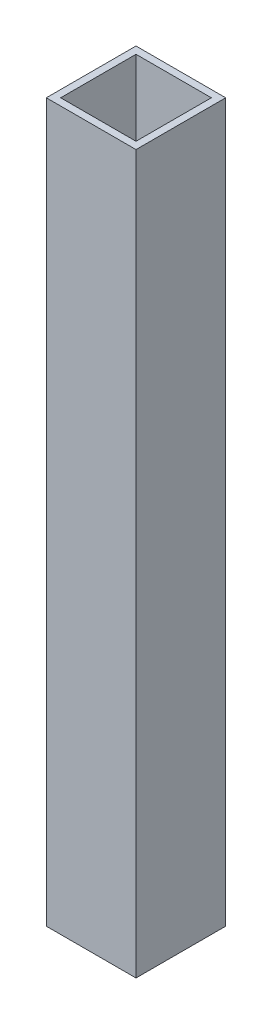
SolidWorks part; units mm, degrees
ref_plane "Front Plane" through (0, 0, 0) normal (0, 0, 1) x (1, 0, 0)
ref_plane "Top Plane" through (0, 0, 0) normal (0, 1, 0) x (1, 0, 0)
ref_plane "Right Plane" through (0, 0, 0) normal (1, 0, 0) x (0, 0, -1)
sketch "Sketch1" plane through (0, 0, 0) normal (0, 1, 0) x (1, 0, 0)
  line L0 (-12.5, 12.5) -> (12.5, -12.5) construction
  line L1 (-12.5, 12.5) -> (12.5, 12.5)
  line L2 (-12.5, 12.5) -> (-12.5, -12.5)
  line L3 (-12.5, -12.5) -> (12.5, -12.5)
  line L4 (12.5, 12.5) -> (12.5, -12.5)
  line L5 (-10.5, 10.5) -> (-10.5, -10.5)
  line L6 (-10.5, -10.5) -> (10.5, -10.5)
  line L7 (10.5, 10.5) -> (10.5, -10.5)
  line L8 (-10.5, 10.5) -> (10.5, 10.5)
  dimension "D1" = 25
  dimension "D2" = 2
extrude "Boss-Extrude1" add sketch "Sketch1" along normal blind 200
